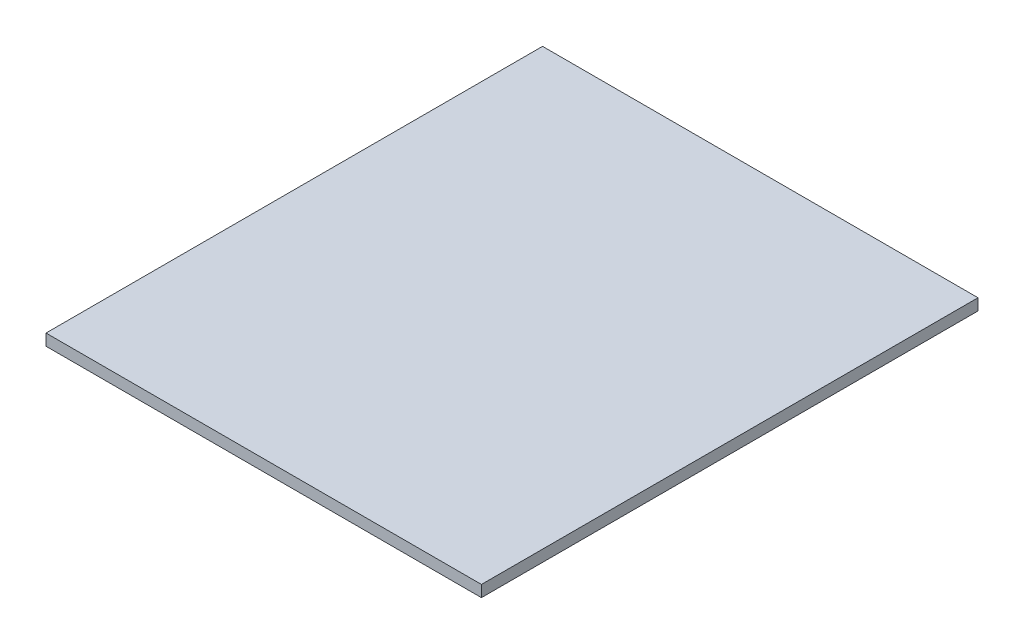
SolidWorks part; units mm, degrees
ref_plane "Front Plane" through (0, 0, 0) normal (0, 0, 1) x (1, 0, 0)
ref_plane "Top Plane" through (0, 0, 0) normal (0, 1, 0) x (1, 0, 0)
ref_plane "Right Plane" through (0, 0, 0) normal (1, 0, 0) x (0, 0, -1)
sketch "Sketch1" plane through (0, 0, 0) normal (0, 1, 0) x (1, 0, 0)
  line L1 (-180, 13) -> (-294, 13)
  line L2 (-180, 13) -> (-180, -117)
  line L3 (-180, -117) -> (-294, -117)
  line L4 (-294, 13) -> (-294, -117)
  dimension "D1" = 130
  dimension "D2" = 114
extrude "Boss-Extrude1" add sketch "Sketch1" along normal blind 3
